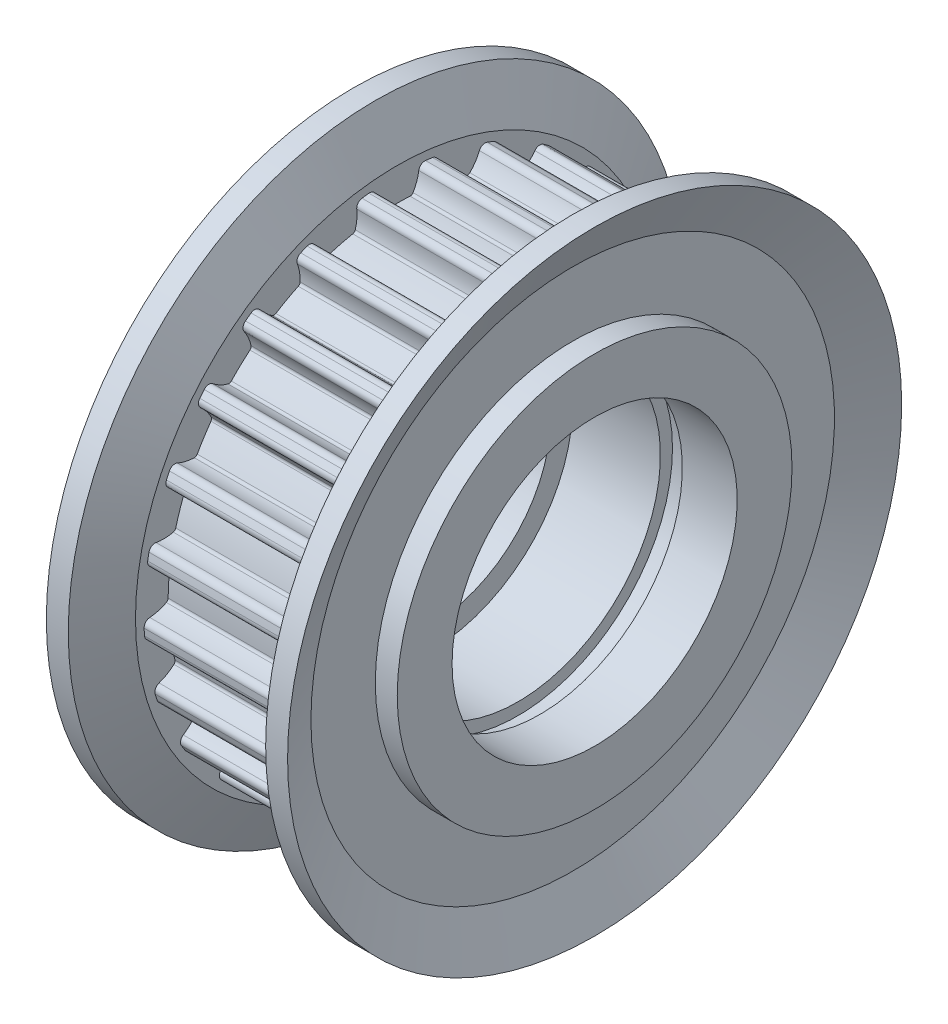
SolidWorks part; units mm, degrees
ref_plane "Front Plane" through (0, 0, 0) normal (0, 0, 1) x (1, 0, 0)
ref_plane "Top Plane" through (0, 0, 0) normal (0, 1, 0) x (1, 0, 0)
ref_plane "Right Plane" through (0, 0, 0) normal (1, 0, 0) x (0, 0, -1)
ref_plane "Plane1" through (0, 0, 0) normal (0, 0, 1) x (1, 0, 0)
sketch "Sketch1" plane through (0, 0, 0) normal (0, 0, 1) x (1, 0, 0)
  line L0 (-5.5, 5.5) -> (-2, 5.5)
  line L1 (-2, 5.5) -> (-2, 6.5)
  line L2 (-2, 6.5) -> (2, 6.5)
  line L3 (2, 6.5) -> (2, 7.05)
  line L4 (2, 7.05) -> (3, 7.05)
  line L5 (3, 7.05) -> (3, 6.5)
  line L6 (3, 6.5) -> (5.5, 6.5)
  line L7 (5.5, 6.5) -> (5.5, 9)
  line L8 (5.5, 9) -> (4.5, 9)
  line L9 (4.5, 9) -> (4.5, 11.935)
  line L10 (4.5, 11.935) -> (5.5, 14)
  line L11 (5.5, 14) -> (4.5, 14)
  line L12 (4.5, 14) -> (3.5, 11.935)
  line L13 (3.5, 11.935) -> (3.5, 11.555)
  line L14 (3.5, 11.555) -> (-3.5, 11.555)
  line L15 (-3.5, 11.555) -> (-3.5, 11.935)
  line L16 (-3.5, 11.935) -> (-4.5, 14)
  line L17 (-4.5, 14) -> (-5.5, 14)
  line L18 (-5.5, 14) -> (-4.5, 11.935)
  line L19 (-4.5, 11.935) -> (-4.5, 9)
  line L20 (-4.5, 9) -> (-5.5, 9)
  line L21 (-5.5, 9) -> (-5.5, 5.5)
  line L22 (11, 0) -> (-11, 0) construction
revolve "Revolve1" add sketch "Sketch1" angle 360 about L22
ref_plane "Plane2" through (3.5, 0, 0) normal (1, 0, 0) x (0, 0, -1)
sketch "Sketch2" plane through (3.5, 0, 0) normal (1, 0, 0) x (0, 0, -1)
  line L0 (1.2899, 11.4828) -> (1.2899, 12.3452)
  line L1 (-1.2899, 12.3452) -> (-1.2899, 11.4828)
  arc A0 (-1.2899, 11.4828) -> (-0.9813, 11.2429) centre (-1.2587, 11.2045) cw
  arc A1 (-0.9813, 11.2429) -> (-0.7209, 10.5016) centre (0.975, 11.5138) ccw
  arc A2 (-0.7209, 10.5016) -> (-0.5837, 10.4287) centre (-0.5921, 10.5784) ccw
  arc A3 (-0.5837, 10.4287) -> (0.5837, 10.4287) centre (0, 0) cw
  arc A4 (0.5837, 10.4287) -> (0.7209, 10.5016) centre (0.5921, 10.5784) ccw
  arc A5 (0.7209, 10.5016) -> (0.9813, 11.2429) centre (-0.975, 11.5138) ccw
  arc A6 (0.9813, 11.2429) -> (1.2899, 11.4828) centre (1.2587, 11.2045) cw
  arc A7 (1.2899, 12.3452) -> (-1.2899, 12.3452) centre (0, 0) ccw
extrude "Cut-Extrude1" cut sketch "Sketch2" against normal blind 7
ref_plane "Plane3" through (3.5, 0, 0) normal (1, 0, 0) x (0, 0, -1)
sketch "Sketch3" plane through (3.5, 0, 0) normal (1, 0, 0) x (0, 0, -1)
  line L0 (4.1051, 10.8012) -> (4.3195, 11.6365)
  line L1 (1.8207, 12.2781) -> (1.6062, 11.4428)
  arc A0 (1.6062, 11.4428) -> (1.8455, 11.1338) centre (1.5673, 11.1655) cw
  arc A1 (1.8455, 11.1338) -> (1.9134, 10.3509) centre (3.8077, 10.9096) ccw
  arc A2 (1.9134, 10.3509) -> (2.0281, 10.2462) centre (2.0573, 10.3933) ccw
  arc A3 (2.0281, 10.2462) -> (3.1589, 9.9559) centre (0, 0) cw
  arc A4 (3.1589, 9.9559) -> (3.3099, 9.9924) centre (3.2042, 10.0989) ccw
  arc A5 (3.3099, 9.9924) -> (3.7465, 10.6457) centre (1.919, 11.3945) ccw
  arc A6 (3.7465, 10.6457) -> (4.1051, 10.8012) centre (4.0056, 10.5395) cw
  arc A7 (4.3195, 11.6365) -> (1.8207, 12.2781) centre (0, 0) ccw
extrude "Cut-Extrude2" cut sketch "Sketch3" against normal blind 7
ref_plane "Plane4" through (3.5, 0, 0) normal (1, 0, 0) x (0, 0, -1)
sketch "Sketch4" plane through (3.5, 0, 0) normal (1, 0, 0) x (0, 0, -1)
  line L0 (6.6623, 9.441) -> (7.0777, 10.1967)
  line L1 (4.8169, 11.4396) -> (4.4015, 10.6839)
  arc A0 (4.4015, 10.6839) -> (4.5564, 10.325) centre (4.2948, 10.425) cw
  arc A1 (4.5564, 10.325) -> (4.4275, 9.5499) centre (6.4012, 9.6199) ccw
  arc A2 (4.4275, 9.5499) -> (4.5126, 9.4199) centre (4.5774, 9.5552) ccw
  arc A3 (4.5126, 9.4199) -> (5.5356, 8.8575) centre (0, 0) cw
  arc A4 (5.5356, 8.8575) -> (5.6909, 8.8553) centre (5.6151, 8.9847) ccw
  arc A5 (5.6909, 8.8553) -> (6.2763, 9.3795) centre (4.6924, 10.5593) ccw
  arc A6 (6.2763, 9.3795) -> (6.6623, 9.441) centre (6.5008, 9.2122) cw
  arc A7 (7.0777, 10.1967) -> (4.8169, 11.4396) centre (0, 0) ccw
extrude "Cut-Extrude3" cut sketch "Sketch4" against normal blind 7
ref_plane "Plane5" through (3.5, 0, 0) normal (1, 0, 0) x (0, 0, -1)
sketch "Sketch5" plane through (3.5, 0, 0) normal (1, 0, 0) x (0, 0, -1)
  line L0 (8.8008, 7.4875) -> (9.3912, 8.1162)
  line L1 (7.5105, 9.8823) -> (6.9202, 9.2536)
  arc A0 (6.9202, 9.2536) -> (6.9809, 8.8675) centre (6.7525, 9.0294) cw
  arc A1 (6.9809, 8.8675) -> (6.6633, 8.1488) centre (8.5925, 7.7258) ccw
  arc A2 (6.6633, 8.1488) -> (6.7134, 8.0017) centre (6.8098, 8.1167) ccw
  arc A3 (6.7134, 8.0017) -> (7.5644, 7.2026) centre (0, 0) cw
  arc A4 (7.5644, 7.2026) -> (7.7143, 7.1618) centre (7.6731, 7.306) ccw
  arc A5 (7.7143, 7.1618) -> (8.4117, 7.524) centre (7.171, 9.0606) ccw
  arc A6 (8.4117, 7.524) -> (8.8008, 7.4875) centre (8.5876, 7.3061) cw
  arc A7 (9.3912, 8.1162) -> (7.5105, 9.8823) centre (0, 0) ccw
extrude "Cut-Extrude4" cut sketch "Sketch5" against normal blind 7
ref_plane "Plane6" through (3.5, 0, 0) normal (1, 0, 0) x (0, 0, -1)
sketch "Sketch6" plane through (3.5, 0, 0) normal (1, 0, 0) x (0, 0, -1)
  line L0 (10.3864, 5.0636) -> (11.1146, 5.5257)
  line L1 (9.7322, 7.704) -> (9.004, 7.2419)
  arc A0 (9.004, 7.2419) -> (8.9669, 6.8528) centre (8.7859, 7.0664) cw
  arc A1 (8.9669, 6.8528) -> (8.4805, 6.2357) centre (10.2438, 5.3462) ccw
  arc A2 (8.4805, 6.2357) -> (8.4925, 6.0808) centre (8.6144, 6.1681) ccw
  arc A3 (8.4925, 6.0808) -> (9.118, 5.0951) centre (0, 0) cw
  arc A4 (9.118, 5.0951) -> (9.253, 5.0184) centre (9.2489, 5.1683) ccw
  arc A5 (9.253, 5.0184) -> (10.0185, 5.1957) centre (9.199, 6.9926) ccw
  arc A6 (10.0185, 5.1957) -> (10.3864, 5.0636) centre (10.1347, 4.9409) cw
  arc A7 (11.1146, 5.5257) -> (9.7322, 7.704) centre (0, 0) ccw
extrude "Cut-Extrude5" cut sketch "Sketch6" against normal blind 7
ref_plane "Plane7" through (3.5, 0, 0) normal (1, 0, 0) x (0, 0, -1)
sketch "Sketch7" plane through (3.5, 0, 0) normal (1, 0, 0) x (0, 0, -1)
  line L0 (11.3194, 2.3216) -> (12.1396, 2.5881)
  line L1 (11.3424, 5.0417) -> (10.5221, 4.7752)
  arc A0 (10.5221, 4.7752) -> (10.3894, 4.4076) centre (10.2672, 4.6595) cw
  arc A1 (10.3894, 4.4076) -> (9.7648, 3.9308) centre (11.2516, 2.6307) ccw
  arc A2 (9.7648, 3.9308) -> (9.7379, 3.7778) centre (9.8777, 3.832) ccw
  arc A3 (9.7379, 3.7778) -> (10.0986, 2.6675) centre (0, 0) cw
  arc A4 (10.0986, 2.6675) -> (10.2103, 2.5596) centre (10.2437, 2.7058) ccw
  arc A5 (10.2103, 2.5596) -> (10.9959, 2.5409) centre (10.649, 4.4852) ccw
  arc A6 (10.9959, 2.5409) -> (11.3194, 2.3216) centre (11.0451, 2.2653) cw
  arc A7 (12.1396, 2.5881) -> (11.3424, 5.0417) centre (0, 0) ccw
extrude "Cut-Extrude6" cut sketch "Sketch7" against normal blind 7
ref_plane "Plane8" through (3.5, 0, 0) normal (1, 0, 0) x (0, 0, -1)
sketch "Sketch8" plane through (3.5, 0, 0) normal (1, 0, 0) x (0, 0, -1)
  line L0 (11.5411, -0.5664) -> (12.4018, -0.5122)
  line L1 (12.2398, 2.0626) -> (11.3791, 2.0084)
  arc A0 (11.3791, 2.0084) -> (11.1591, 1.6853) centre (11.1034, 1.9597) cw
  arc A1 (11.1591, 1.6853) -> (10.4356, 1.3789) centre (11.5523, -0.2501) ccw
  arc A2 (10.4356, 1.3789) -> (10.3714, 1.2374) centre (10.5204, 1.2551) ccw
  arc A3 (10.3714, 1.2374) -> (10.4447, 0.0723) centre (0, 0) cw
  arc A4 (10.4447, 0.0723) -> (10.5261, -0.0601) centre (10.5947, 0.0733) ccw
  arc A5 (10.5261, -0.0601) -> (11.2824, -0.2735) centre (11.4299, 1.696) ccw
  arc A6 (11.2824, -0.2735) -> (11.5411, -0.5664) centre (11.2614, -0.5527) cw
  arc A7 (12.4018, -0.5122) -> (12.2398, 2.0626) centre (0, 0) ccw
extrude "Cut-Extrude7" cut sketch "Sketch8" against normal blind 7
ref_plane "Plane9" through (3.5, 0, 0) normal (1, 0, 0) x (0, 0, -1)
sketch "Sketch9" plane through (3.5, 0, 0) normal (1, 0, 0) x (0, 0, -1)
  line L0 (11.0377, -3.4188) -> (11.8848, -3.5804)
  line L1 (12.3682, -1.0462) -> (11.5211, -0.8846)
  arc A0 (11.5211, -0.8846) -> (11.2277, -1.1428) centre (11.2419, -0.8631) cw
  arc A1 (11.2277, -1.1428) -> (10.4506, -1.2597) centre (11.1272, -3.1152) ccw
  arc A2 (10.4506, -1.2597) -> (10.3533, -1.3808) centre (10.502, -1.4006) ccw
  arc A3 (10.3533, -1.3808) -> (10.1346, -2.5275) centre (0, 0) cw
  arc A4 (10.1346, -2.5275) -> (10.1805, -2.6759) centre (10.2801, -2.5638) ccw
  arc A5 (10.1805, -2.6759) -> (10.8599, -3.0707) centre (11.4925, -1.1997) ccw
  arc A6 (10.8599, -3.0707) -> (11.0377, -3.4188) centre (10.7702, -3.3359) cw
  arc A7 (11.8848, -3.5804) -> (12.3682, -1.0462) centre (0, 0) ccw
extrude "Cut-Extrude8" cut sketch "Sketch9" against normal blind 7
ref_plane "Plane10" through (3.5, 0, 0) normal (1, 0, 0) x (0, 0, -1)
sketch "Sketch10" plane through (3.5, 0, 0) normal (1, 0, 0) x (0, 0, -1)
  line L0 (9.8407, -6.0563) -> (10.621, -6.4235)
  line L1 (11.7195, -4.0891) -> (10.9392, -3.7219)
  arc A0 (10.9392, -3.7219) -> (10.5907, -3.8991) centre (10.6741, -3.6318) cw
  arc A1 (10.5907, -3.8991) -> (9.809, -3.8191) centre (10.0029, -5.7845) ccw
  arc A2 (9.809, -3.8191) -> (9.6847, -3.9122) centre (9.8238, -3.9683) ccw
  arc A3 (9.6847, -3.9122) -> (9.1876, -4.9685) centre (0, 0) cw
  arc A4 (9.1876, -4.9685) -> (9.1952, -5.1236) centre (9.3196, -5.0398) ccw
  arc A5 (9.1952, -5.1236) -> (9.7551, -5.6749) centre (10.8331, -4.0201) ccw
  arc A6 (9.7551, -5.6749) -> (9.8407, -6.0563) centre (9.6022, -5.9096) cw
  arc A7 (10.621, -6.4235) -> (11.7195, -4.0891) centre (0, 0) ccw
extrude "Cut-Extrude9" cut sketch "Sketch10" against normal blind 7
ref_plane "Plane11" through (3.5, 0, 0) normal (1, 0, 0) x (0, 0, -1)
sketch "Sketch11" plane through (3.5, 0, 0) normal (1, 0, 0) x (0, 0, -1)
  line L0 (8.0254, -8.3133) -> (8.6899, -8.863)
  line L1 (10.3344, -6.8752) -> (9.6699, -6.3255)
  arc A0 (9.6699, -6.3255) -> (9.2883, -6.4104) centre (9.4356, -6.1722) cw
  arc A1 (9.2883, -6.4104) -> (8.5511, -6.1385) centre (8.25, -8.0904) ccw
  arc A2 (8.5511, -6.1385) -> (8.4075, -6.1977) centre (8.5282, -6.2867) ccw
  arc A3 (8.4075, -6.1977) -> (7.6634, -7.0972) centre (0, 0) cw
  arc A4 (7.6634, -7.0972) -> (7.6321, -7.2494) centre (7.7734, -7.1992) ccw
  arc A5 (7.6321, -7.2494) -> (8.0373, -7.9226) centre (9.493, -6.5879) ccw
  arc A6 (8.0373, -7.9226) -> (8.0254, -8.3133) centre (7.8309, -8.1119) cw
  arc A7 (8.6899, -8.863) -> (10.3344, -6.8752) centre (0, 0) ccw
extrude "Cut-Extrude10" cut sketch "Sketch11" against normal blind 7
ref_plane "Plane12" through (3.5, 0, 0) normal (1, 0, 0) x (0, 0, -1)
sketch "Sketch12" plane through (3.5, 0, 0) normal (1, 0, 0) x (0, 0, -1)
  line L0 (5.7058, -10.048) -> (6.2127, -10.7457)
  line L1 (8.2999, -9.2293) -> (7.793, -8.5315)
  arc A0 (7.793, -8.5315) -> (7.4023, -8.5189) centre (7.6042, -8.3248) cw
  arc A1 (7.4023, -8.5189) -> (6.7559, -8.0722) centre (5.9788, -9.8879) ccw
  arc A2 (6.7559, -8.0722) -> (6.602, -8.0939) centre (6.6969, -8.2101) ccw
  arc A3 (6.602, -8.0939) -> (5.6576, -8.7801) centre (0, 0) cw
  arc A4 (5.6576, -8.7801) -> (5.5895, -8.9197) centre (5.7388, -8.9062) ccw
  arc A5 (5.5895, -8.9197) -> (5.8145, -9.6725) centre (7.5564, -8.7418) ccw
  arc A6 (5.8145, -9.6725) -> (5.7058, -10.048) centre (5.5676, -9.8045) cw
  arc A7 (6.2127, -10.7457) -> (8.2999, -9.2293) centre (0, 0) ccw
extrude "Cut-Extrude11" cut sketch "Sketch12" against normal blind 7
ref_plane "Plane13" through (3.5, 0, 0) normal (1, 0, 0) x (0, 0, -1)
sketch "Sketch13" plane through (3.5, 0, 0) normal (1, 0, 0) x (0, 0, -1)
  line L0 (3.0277, -11.1513) -> (3.3452, -11.9531)
  line L1 (5.7439, -11.0034) -> (5.4265, -10.2015)
  arc A0 (5.4265, -10.2015) -> (5.0512, -10.0922) centre (5.295, -9.9543) cw
  arc A1 (5.0512, -10.0922) -> (4.5361, -9.4987) centre (3.332, -11.0642) ccw
  arc A2 (4.5361, -9.4987) -> (4.3818, -9.4815) centre (4.4447, -9.6176) ccw
  arc A3 (4.3818, -9.4815) -> (3.2963, -9.9112) centre (0, 0) cw
  arc A4 (3.2963, -9.9112) -> (3.1956, -10.0295) centre (3.3437, -10.0535) ccw
  arc A5 (3.1956, -10.0295) -> (3.2264, -10.8147) centre (5.145, -10.3463) ccw
  arc A6 (3.2264, -10.8147) -> (3.0277, -11.1513) centre (2.9544, -10.8811) cw
  arc A7 (3.3452, -11.9531) -> (5.7439, -11.0034) centre (0, 0) ccw
extrude "Cut-Extrude12" cut sketch "Sketch13" against normal blind 7
ref_plane "Plane14" through (3.5, 0, 0) normal (1, 0, 0) x (0, 0, -1)
sketch "Sketch14" plane through (3.5, 0, 0) normal (1, 0, 0) x (0, 0, -1)
  line L0 (0.1594, -11.5539) -> (0.2675, -12.4095)
  line L1 (2.827, -12.0862) -> (2.719, -11.2306)
  arc A0 (2.719, -11.2306) -> (2.3827, -11.0313) centre (2.6531, -10.9584) cw
  arc A1 (2.3827, -11.0313) -> (2.0314, -10.3284) centre (0.4757, -11.5452) ccw
  arc A2 (2.0314, -10.3284) -> (1.8862, -10.2733) centre (1.9132, -10.4208) ccw
  arc A3 (1.8862, -10.2733) -> (0.728, -10.4196) centre (0, 0) cw
  arc A4 (0.728, -10.4196) -> (0.601, -10.5091) centre (0.7384, -10.5692) ccw
  arc A5 (0.601, -10.5091) -> (0.4355, -11.2773) centre (2.4104, -11.3008) ccw
  arc A6 (0.4355, -11.2773) -> (0.1594, -11.5539) centre (0.1555, -11.2739) cw
  arc A7 (0.2675, -12.4095) -> (2.827, -12.0862) centre (0, 0) ccw
extrude "Cut-Extrude13" cut sketch "Sketch14" against normal blind 7
ref_plane "Plane15" through (3.5, 0, 0) normal (1, 0, 0) x (0, 0, -1)
sketch "Sketch15" plane through (3.5, 0, 0) normal (1, 0, 0) x (0, 0, -1)
  line L0 (-2.719, -11.2306) -> (-2.827, -12.0862)
  line L1 (-0.2675, -12.4095) -> (-0.1594, -11.5539)
  arc A0 (-0.1594, -11.5539) -> (-0.4355, -11.2773) centre (-0.1555, -11.2739) cw
  arc A1 (-0.4355, -11.2773) -> (-0.601, -10.5091) centre (-2.4104, -11.3008) ccw
  arc A2 (-0.601, -10.5091) -> (-0.728, -10.4196) centre (-0.7384, -10.5692) ccw
  arc A3 (-0.728, -10.4196) -> (-1.8862, -10.2733) centre (0, 0) cw
  arc A4 (-1.8862, -10.2733) -> (-2.0314, -10.3284) centre (-1.9132, -10.4208) ccw
  arc A5 (-2.0314, -10.3284) -> (-2.3827, -11.0313) centre (-0.4757, -11.5452) ccw
  arc A6 (-2.3827, -11.0313) -> (-2.719, -11.2306) centre (-2.6531, -10.9584) cw
  arc A7 (-2.827, -12.0862) -> (-0.2675, -12.4095) centre (0, 0) ccw
extrude "Cut-Extrude14" cut sketch "Sketch15" against normal blind 7
ref_plane "Plane16" through (3.5, 0, 0) normal (1, 0, 0) x (0, 0, -1)
sketch "Sketch16" plane through (3.5, 0, 0) normal (1, 0, 0) x (0, 0, -1)
  line L0 (-5.4265, -10.2015) -> (-5.7439, -11.0034)
  line L1 (-3.3452, -11.9531) -> (-3.0277, -11.1513)
  arc A0 (-3.0277, -11.1513) -> (-3.2264, -10.8147) centre (-2.9544, -10.8811) cw
  arc A1 (-3.2264, -10.8147) -> (-3.1956, -10.0295) centre (-5.145, -10.3463) ccw
  arc A2 (-3.1956, -10.0295) -> (-3.2963, -9.9112) centre (-3.3437, -10.0535) ccw
  arc A3 (-3.2963, -9.9112) -> (-4.3818, -9.4815) centre (0, 0) cw
  arc A4 (-4.3818, -9.4815) -> (-4.5361, -9.4987) centre (-4.4447, -9.6176) ccw
  arc A5 (-4.5361, -9.4987) -> (-5.0512, -10.0922) centre (-3.332, -11.0642) ccw
  arc A6 (-5.0512, -10.0922) -> (-5.4265, -10.2015) centre (-5.295, -9.9543) cw
  arc A7 (-5.7439, -11.0034) -> (-3.3452, -11.9531) centre (0, 0) ccw
extrude "Cut-Extrude15" cut sketch "Sketch16" against normal blind 7
ref_plane "Plane17" through (3.5, 0, 0) normal (1, 0, 0) x (0, 0, -1)
sketch "Sketch17" plane through (3.5, 0, 0) normal (1, 0, 0) x (0, 0, -1)
  line L0 (-7.793, -8.5315) -> (-8.2999, -9.2293)
  line L1 (-6.2127, -10.7457) -> (-5.7058, -10.048)
  arc A0 (-5.7058, -10.048) -> (-5.8145, -9.6725) centre (-5.5676, -9.8045) cw
  arc A1 (-5.8145, -9.6725) -> (-5.5895, -8.9197) centre (-7.5564, -8.7418) ccw
  arc A2 (-5.5895, -8.9197) -> (-5.6576, -8.7801) centre (-5.7388, -8.9062) ccw
  arc A3 (-5.6576, -8.7801) -> (-6.602, -8.0939) centre (0, 0) cw
  arc A4 (-6.602, -8.0939) -> (-6.7559, -8.0722) centre (-6.6969, -8.2101) ccw
  arc A5 (-6.7559, -8.0722) -> (-7.4023, -8.5189) centre (-5.9788, -9.8879) ccw
  arc A6 (-7.4023, -8.5189) -> (-7.793, -8.5315) centre (-7.6042, -8.3248) cw
  arc A7 (-8.2999, -9.2293) -> (-6.2127, -10.7457) centre (0, 0) ccw
extrude "Cut-Extrude16" cut sketch "Sketch17" against normal blind 7
ref_plane "Plane18" through (3.5, 0, 0) normal (1, 0, 0) x (0, 0, -1)
sketch "Sketch18" plane through (3.5, 0, 0) normal (1, 0, 0) x (0, 0, -1)
  line L0 (-9.6699, -6.3255) -> (-10.3344, -6.8752)
  line L1 (-8.6899, -8.863) -> (-8.0254, -8.3133)
  arc A0 (-8.0254, -8.3133) -> (-8.0373, -7.9226) centre (-7.8309, -8.1119) cw
  arc A1 (-8.0373, -7.9226) -> (-7.6321, -7.2494) centre (-9.493, -6.5879) ccw
  arc A2 (-7.6321, -7.2494) -> (-7.6634, -7.0972) centre (-7.7734, -7.1992) ccw
  arc A3 (-7.6634, -7.0972) -> (-8.4075, -6.1977) centre (0, 0) cw
  arc A4 (-8.4075, -6.1977) -> (-8.5511, -6.1385) centre (-8.5282, -6.2867) ccw
  arc A5 (-8.5511, -6.1385) -> (-9.2883, -6.4104) centre (-8.25, -8.0904) ccw
  arc A6 (-9.2883, -6.4104) -> (-9.6699, -6.3255) centre (-9.4356, -6.1722) cw
  arc A7 (-10.3344, -6.8752) -> (-8.6899, -8.863) centre (0, 0) ccw
extrude "Cut-Extrude17" cut sketch "Sketch18" against normal blind 7
ref_plane "Plane19" through (3.5, 0, 0) normal (1, 0, 0) x (0, 0, -1)
sketch "Sketch19" plane through (3.5, 0, 0) normal (1, 0, 0) x (0, 0, -1)
  line L0 (-10.9392, -3.7219) -> (-11.7195, -4.0891)
  line L1 (-10.621, -6.4235) -> (-9.8407, -6.0563)
  arc A0 (-9.8407, -6.0563) -> (-9.7551, -5.6749) centre (-9.6022, -5.9096) cw
  arc A1 (-9.7551, -5.6749) -> (-9.1952, -5.1236) centre (-10.8331, -4.0201) ccw
  arc A2 (-9.1952, -5.1236) -> (-9.1876, -4.9685) centre (-9.3196, -5.0398) ccw
  arc A3 (-9.1876, -4.9685) -> (-9.6847, -3.9122) centre (0, 0) cw
  arc A4 (-9.6847, -3.9122) -> (-9.809, -3.8191) centre (-9.8238, -3.9683) ccw
  arc A5 (-9.809, -3.8191) -> (-10.5907, -3.8991) centre (-10.0029, -5.7845) ccw
  arc A6 (-10.5907, -3.8991) -> (-10.9392, -3.7219) centre (-10.6741, -3.6318) cw
  arc A7 (-11.7195, -4.0891) -> (-10.621, -6.4235) centre (0, 0) ccw
extrude "Cut-Extrude18" cut sketch "Sketch19" against normal blind 7
ref_plane "Plane20" through (3.5, 0, 0) normal (1, 0, 0) x (0, 0, -1)
sketch "Sketch20" plane through (3.5, 0, 0) normal (1, 0, 0) x (0, 0, -1)
  line L0 (-11.5211, -0.8846) -> (-12.3682, -1.0462)
  line L1 (-11.8848, -3.5804) -> (-11.0377, -3.4188)
  arc A0 (-11.0377, -3.4188) -> (-10.8599, -3.0707) centre (-10.7702, -3.3359) cw
  arc A1 (-10.8599, -3.0707) -> (-10.1805, -2.6759) centre (-11.4925, -1.1997) ccw
  arc A2 (-10.1805, -2.6759) -> (-10.1346, -2.5275) centre (-10.2801, -2.5638) ccw
  arc A3 (-10.1346, -2.5275) -> (-10.3533, -1.3808) centre (0, 0) cw
  arc A4 (-10.3533, -1.3808) -> (-10.4506, -1.2597) centre (-10.502, -1.4006) ccw
  arc A5 (-10.4506, -1.2597) -> (-11.2277, -1.1428) centre (-11.1272, -3.1152) ccw
  arc A6 (-11.2277, -1.1428) -> (-11.5211, -0.8846) centre (-11.2419, -0.8631) cw
  arc A7 (-12.3682, -1.0462) -> (-11.8848, -3.5804) centre (0, 0) ccw
extrude "Cut-Extrude19" cut sketch "Sketch20" against normal blind 7
ref_plane "Plane21" through (3.5, 0, 0) normal (1, 0, 0) x (0, 0, -1)
sketch "Sketch21" plane through (3.5, 0, 0) normal (1, 0, 0) x (0, 0, -1)
  line L0 (-11.3791, 2.0084) -> (-12.2398, 2.0626)
  line L1 (-12.4018, -0.5122) -> (-11.5411, -0.5664)
  arc A0 (-11.5411, -0.5664) -> (-11.2824, -0.2735) centre (-11.2614, -0.5527) cw
  arc A1 (-11.2824, -0.2735) -> (-10.5261, -0.0601) centre (-11.4299, 1.696) ccw
  arc A2 (-10.5261, -0.0601) -> (-10.4447, 0.0723) centre (-10.5947, 0.0733) ccw
  arc A3 (-10.4447, 0.0723) -> (-10.3714, 1.2374) centre (0, 0) cw
  arc A4 (-10.3714, 1.2374) -> (-10.4356, 1.3789) centre (-10.5204, 1.2551) ccw
  arc A5 (-10.4356, 1.3789) -> (-11.1591, 1.6853) centre (-11.5523, -0.2501) ccw
  arc A6 (-11.1591, 1.6853) -> (-11.3791, 2.0084) centre (-11.1034, 1.9597) cw
  arc A7 (-12.2398, 2.0626) -> (-12.4018, -0.5122) centre (0, 0) ccw
extrude "Cut-Extrude20" cut sketch "Sketch21" against normal blind 7
ref_plane "Plane22" through (3.5, 0, 0) normal (1, 0, 0) x (0, 0, -1)
sketch "Sketch22" plane through (3.5, 0, 0) normal (1, 0, 0) x (0, 0, -1)
  line L0 (-10.5221, 4.7752) -> (-11.3424, 5.0417)
  line L1 (-12.1396, 2.5881) -> (-11.3194, 2.3216)
  arc A0 (-11.3194, 2.3216) -> (-10.9959, 2.5409) centre (-11.0451, 2.2653) cw
  arc A1 (-10.9959, 2.5409) -> (-10.2103, 2.5596) centre (-10.649, 4.4852) ccw
  arc A2 (-10.2103, 2.5596) -> (-10.0986, 2.6675) centre (-10.2437, 2.7058) ccw
  arc A3 (-10.0986, 2.6675) -> (-9.7379, 3.7778) centre (0, 0) cw
  arc A4 (-9.7379, 3.7778) -> (-9.7648, 3.9308) centre (-9.8777, 3.832) ccw
  arc A5 (-9.7648, 3.9308) -> (-10.3894, 4.4076) centre (-11.2516, 2.6307) ccw
  arc A6 (-10.3894, 4.4076) -> (-10.5221, 4.7752) centre (-10.2672, 4.6595) cw
  arc A7 (-11.3424, 5.0417) -> (-12.1396, 2.5881) centre (0, 0) ccw
extrude "Cut-Extrude21" cut sketch "Sketch22" against normal blind 7
ref_plane "Plane23" through (3.5, 0, 0) normal (1, 0, 0) x (0, 0, -1)
sketch "Sketch23" plane through (3.5, 0, 0) normal (1, 0, 0) x (0, 0, -1)
  line L0 (-9.004, 7.2419) -> (-9.7322, 7.704)
  line L1 (-11.1146, 5.5257) -> (-10.3864, 5.0636)
  arc A0 (-10.3864, 5.0636) -> (-10.0185, 5.1957) centre (-10.1347, 4.9409) cw
  arc A1 (-10.0185, 5.1957) -> (-9.253, 5.0184) centre (-9.199, 6.9926) ccw
  arc A2 (-9.253, 5.0184) -> (-9.118, 5.0951) centre (-9.2489, 5.1683) ccw
  arc A3 (-9.118, 5.0951) -> (-8.4925, 6.0808) centre (0, 0) cw
  arc A4 (-8.4925, 6.0808) -> (-8.4805, 6.2357) centre (-8.6144, 6.1681) ccw
  arc A5 (-8.4805, 6.2357) -> (-8.9669, 6.8528) centre (-10.2438, 5.3462) ccw
  arc A6 (-8.9669, 6.8528) -> (-9.004, 7.2419) centre (-8.7859, 7.0664) cw
  arc A7 (-9.7322, 7.704) -> (-11.1146, 5.5257) centre (0, 0) ccw
extrude "Cut-Extrude22" cut sketch "Sketch23" against normal blind 7
ref_plane "Plane24" through (3.5, 0, 0) normal (1, 0, 0) x (0, 0, -1)
sketch "Sketch24" plane through (3.5, 0, 0) normal (1, 0, 0) x (0, 0, -1)
  line L0 (-6.9202, 9.2536) -> (-7.5105, 9.8823)
  line L1 (-9.3912, 8.1162) -> (-8.8008, 7.4875)
  arc A0 (-8.8008, 7.4875) -> (-8.4117, 7.524) centre (-8.5876, 7.3061) cw
  arc A1 (-8.4117, 7.524) -> (-7.7143, 7.1618) centre (-7.171, 9.0606) ccw
  arc A2 (-7.7143, 7.1618) -> (-7.5644, 7.2026) centre (-7.6731, 7.306) ccw
  arc A3 (-7.5644, 7.2026) -> (-6.7134, 8.0017) centre (0, 0) cw
  arc A4 (-6.7134, 8.0017) -> (-6.6633, 8.1488) centre (-6.8098, 8.1167) ccw
  arc A5 (-6.6633, 8.1488) -> (-6.9809, 8.8675) centre (-8.5925, 7.7258) ccw
  arc A6 (-6.9809, 8.8675) -> (-6.9202, 9.2536) centre (-6.7525, 9.0294) cw
  arc A7 (-7.5105, 9.8823) -> (-9.3912, 8.1162) centre (0, 0) ccw
extrude "Cut-Extrude23" cut sketch "Sketch24" against normal blind 7
ref_plane "Plane25" through (3.5, 0, 0) normal (1, 0, 0) x (0, 0, -1)
sketch "Sketch25" plane through (3.5, 0, 0) normal (1, 0, 0) x (0, 0, -1)
  line L0 (-4.4015, 10.6839) -> (-4.8169, 11.4396)
  line L1 (-7.0777, 10.1967) -> (-6.6623, 9.441)
  arc A0 (-6.6623, 9.441) -> (-6.2763, 9.3795) centre (-6.5008, 9.2122) cw
  arc A1 (-6.2763, 9.3795) -> (-5.6909, 8.8553) centre (-4.6924, 10.5593) ccw
  arc A2 (-5.6909, 8.8553) -> (-5.5356, 8.8575) centre (-5.6151, 8.9847) ccw
  arc A3 (-5.5356, 8.8575) -> (-4.5126, 9.4199) centre (0, 0) cw
  arc A4 (-4.5126, 9.4199) -> (-4.4275, 9.5499) centre (-4.5774, 9.5552) ccw
  arc A5 (-4.4275, 9.5499) -> (-4.5564, 10.325) centre (-6.4012, 9.6199) ccw
  arc A6 (-4.5564, 10.325) -> (-4.4015, 10.6839) centre (-4.2948, 10.425) cw
  arc A7 (-4.8169, 11.4396) -> (-7.0777, 10.1967) centre (0, 0) ccw
extrude "Cut-Extrude24" cut sketch "Sketch25" against normal blind 7
ref_plane "Plane26" through (3.5, 0, 0) normal (1, 0, 0) x (0, 0, -1)
sketch "Sketch26" plane through (3.5, 0, 0) normal (1, 0, 0) x (0, 0, -1)
  line L0 (-1.6062, 11.4428) -> (-1.8207, 12.2781)
  line L1 (-4.3195, 11.6365) -> (-4.1051, 10.8012)
  arc A0 (-4.1051, 10.8012) -> (-3.7465, 10.6457) centre (-4.0056, 10.5395) cw
  arc A1 (-3.7465, 10.6457) -> (-3.3099, 9.9924) centre (-1.919, 11.3945) ccw
  arc A2 (-3.3099, 9.9924) -> (-3.1589, 9.9559) centre (-3.2042, 10.0989) ccw
  arc A3 (-3.1589, 9.9559) -> (-2.0281, 10.2462) centre (0, 0) cw
  arc A4 (-2.0281, 10.2462) -> (-1.9134, 10.3509) centre (-2.0573, 10.3933) ccw
  arc A5 (-1.9134, 10.3509) -> (-1.8455, 11.1338) centre (-3.8077, 10.9096) ccw
  arc A6 (-1.8455, 11.1338) -> (-1.6062, 11.4428) centre (-1.5673, 11.1655) cw
  arc A7 (-1.8207, 12.2781) -> (-4.3195, 11.6365) centre (0, 0) ccw
extrude "Cut-Extrude25" cut sketch "Sketch26" against normal blind 7
